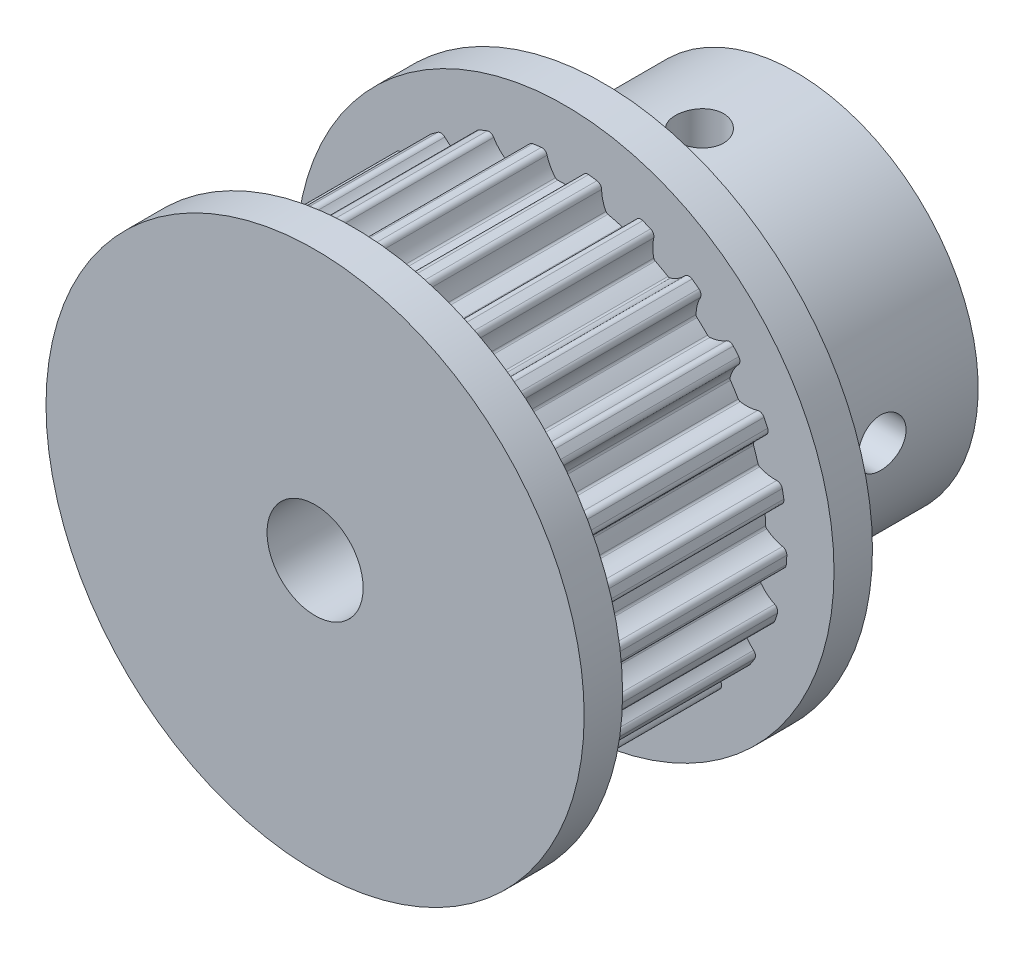
SolidWorks part; units mm, degrees
material "6061-T6 (SS)"
ref_plane "前基準面" through (0, 0, 0) normal (0, 0, 1) x (1, 0, 0)
ref_plane "上基準面" through (0, 0, 0) normal (0, 1, 0) x (1, 0, 0)
ref_plane "右基準面" through (0, 0, 0) normal (1, 0, 0) x (0, 0, -1)
sketch "草圖1" plane through (0, 0, 0) normal (0, 0, 1) x (1, 0, 0)
  circle A0 centre (0, 0) radius 11.555
  dimension "D1" = 23.11
extrude "填料-伸長1" add sketch "草圖1" along normal mid plane 11
sketch "草圖2" plane through (0, 0, 5.5) normal (0, 0, 1) x (1, 0, 0)
  line L0 (0, 0) -> (0, 11.809) construction
  line L1 (-0.975, 11.809) -> (0.975, 11.809) construction
  arc A0 (-0.3761, 10.4382) -> (0.3761, 10.4382) centre (0, 0) cw
  circle A1 centre (0, 0) radius 11.555 construction
  arc A2 (-1.2291, 11.4894) -> (-0.9293, 11.2853) centre (-1.1993, 11.211) cw
  arc A3 (-0.9293, 11.2853) -> (-0.493, 10.4878) centre (0.975, 11.809) ccw
  arc A4 (-0.493, 10.4878) -> (-0.3761, 10.4382) centre (-0.3815, 10.5881) ccw
  arc A5 (0.493, 10.4878) -> (0.3761, 10.4382) centre (0.3815, 10.5881) cw
  arc A6 (0.9293, 11.2853) -> (0.493, 10.4878) centre (-0.975, 11.809) cw
  arc A7 (1.2291, 11.4894) -> (0.9293, 11.2853) centre (1.1993, 11.211) ccw
  point P6 (0, 10.445)
  point P18 (0, 11.555)
  dimension "D1" = 1.11
  dimension "D2" = 0.15
  dimension "D3" = 1.975
  dimension "D4" = 0.28
  dimension "D5" = 1.95
  dimension "D6" = 0.254
extrude "除料-伸長1" cut sketch "草圖2" against normal through all and the other way through all flip side to cut
pattern_circular "環狀複製排列1" count 25 over 360 about axis through (0, 0, 5.5) along (0, 0, 1) of "除料-伸長1"
sketch "草圖3" plane through (0, 0, 5.5) normal (0, 0, 1) x (1, 0, 0)
  circle A0 centre (0, 0) radius 14
  dimension "D1" = 28
extrude "填料-伸長2" add sketch "草圖3" along normal blind 2
mirror "鏡射1" about plane through (0, 0, 0) normal (0, 0, 1) of "填料-伸長2"
sketch "草圖5" plane through (0, 0, -7.5) normal (0, 0, -1) x (-1, 0, 0)
  circle A0 centre (0, 0) radius 9.5
  dimension "D1" = 19
extrude "填料-伸長3" add sketch "草圖5" along normal blind 10
sketch "草圖4" plane through (0, 0, 7.5) normal (0, 0, 1) x (1, 0, 0)
  circle A0 centre (0, 0) radius 2.5
  dimension "D1" = 5
extrude "除料-伸長2" cut sketch "草圖4" against normal through all
hole_wizard "M3x0.5 螺紋孔1" positions "草圖6" profile "草圖7" tap size "M3x0.5" standard "Ansi Metric"
sketch "草圖6" plane through (0, 0, 0) normal (0, 1, 0) x (1, 0, 0)
  point P0 (0, 12.5)
sketch "草圖7" plane through (0, 0, -12.5) normal (1, 0, 0) x (0, 0, -1)
  line L0 (0, 0) -> (0, 14)
  line L1 (0, 14) -> (1.25, 14)
  line L2 (1.25, 14) -> (1.25, 0)
  line L5 (1.25, 0) -> (0, 0)
  line L11 (0, -6.35) -> (0, 107.95) construction
  dimension "貫穿螺孔鑽直徑" = 2.5
  dimension "貫穿螺孔鑽深度" = 14
pattern_circular "環狀複製排列2" count 2 every 90 about axis through (0, 0, -17.5) along (0, 0, -1) of "M3x0.5 螺紋孔1"
